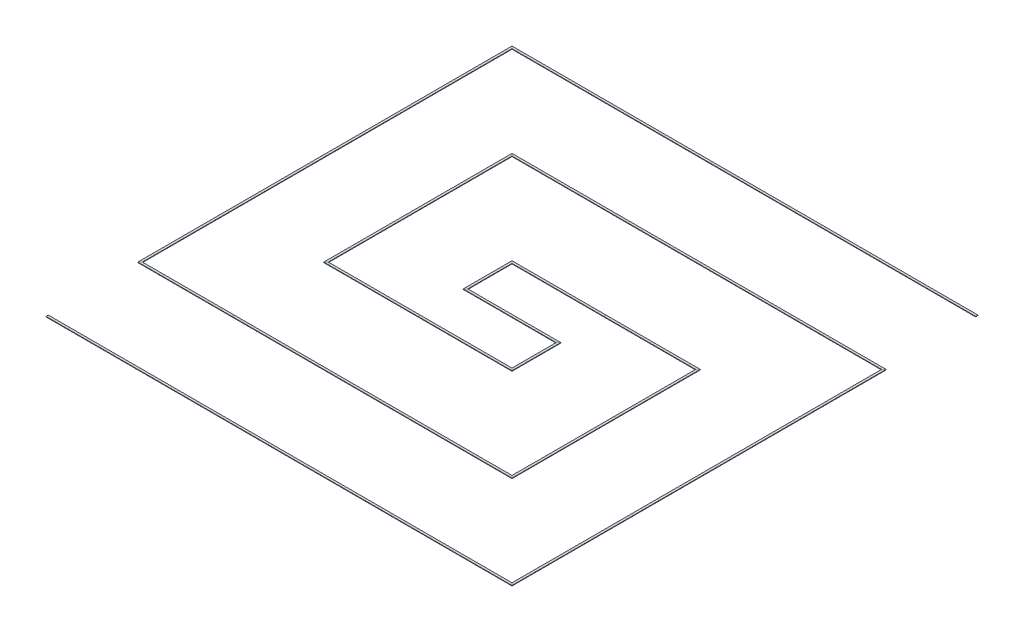
SolidWorks part; units mm, degrees
ref_plane "Front Plane" through (0, 0, 0) normal (0, 0, 1) x (1, 0, 0)
ref_plane "Top Plane" through (0, 0, 0) normal (0, 1, 0) x (1, 0, 0)
ref_plane "Right Plane" through (0, 0, 0) normal (1, 0, 0) x (0, 0, -1)
sketch "Sketch2" plane through (0, 0, 0) normal (0, 1, 0) x (1, 0, 0)
  line L0 (-0.5, 0) -> (0.5, 0)
  line L1 (-2.5, -2.5) -> (2.5, -2.5)
  line L2 (-2.5, -1.5) -> (-2.5, 2.5)
  line L3 (-2.5, 2.5) -> (2.5, 2.5)
  line L4 (2.5, -2.5) -> (2.5, 1.5)
  line L5 (-2.5, -2.5) -> (2.5, 2.5) construction
  line L6 (-2.5, 2.5) -> (2.5, -2.5) construction
  line L7 (-1.5, -1.5) -> (1.5, -1.5)
  line L8 (-1.5, -0.5) -> (-1.5, 1.5)
  line L9 (-1.5, 1.5) -> (1.5, 1.5)
  line L10 (1.5, -1.5) -> (1.5, 0.5)
  line L11 (-1.5, -1.5) -> (1.5, 1.5) construction
  line L12 (-1.5, 1.5) -> (1.5, -1.5) construction
  line L13 (-0.5, -0.5) -> (0.5, -0.5)
  line L14 (-0.5, 0) -> (-0.5, 0.5)
  line L15 (-0.5, 0.5) -> (0.5, 0.5)
  line L16 (0.5, -0.5) -> (0.5, 0)
  line L17 (-0.5, -0.5) -> (0.5, 0.5) construction
  line L18 (-0.5, 0.5) -> (0.5, -0.5) construction
  line L19 (-1.5, -1.5) -> (-2.5, -1.5)
  line L20 (-0.5, -0.5) -> (-1.5, -0.5)
  line L21 (0.5, 0.5) -> (1.5, 0.5)
  line L22 (1.5, 1.5) -> (2.5, 1.5)
  point P0 (0, 0)
  point P5 (0, 0)
  point P11 (0, 0)
  dimension "D1" = 5
  dimension "D2" = 3
  dimension "D3" = 1
sketch "Sketch3" plane through (0, 0, 0) normal (1, 0, 0) x (0, 0, -1)
  line L1 (-0.0125, -0.0025) -> (0.0125, -0.0025)
  line L2 (-0.0125, -0.0025) -> (-0.0125, 0.0025)
  line L3 (-0.0125, 0.0025) -> (0.0125, 0.0025)
  line L4 (0.0125, -0.0025) -> (0.0125, 0.0025)
  line L5 (-0.0125, -0.0025) -> (0.0125, 0.0025) construction
  line L6 (-0.0125, 0.0025) -> (0.0125, -0.0025) construction
  point P0 (0, 0)
  dimension "D1" = 0.005
  dimension "D2" = 0.025
sweep "Sweep1" add profiles "Sketch3" path "Sketch2"
